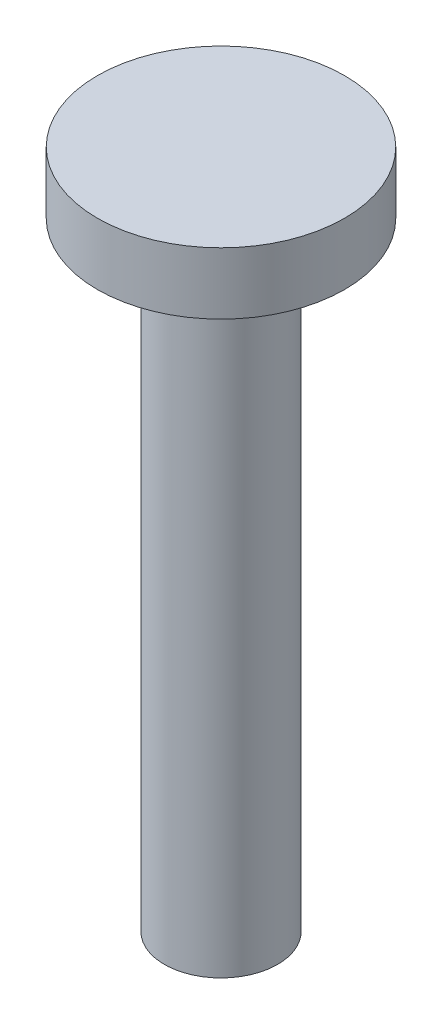
SolidWorks part; units mm, degrees
ref_plane "Front" through (0, 0, 0) normal (0, 0, 1) x (1, 0, 0)
ref_plane "Top" through (0, 0, 0) normal (0, 1, 0) x (1, 0, 0)
ref_plane "Right" through (0, 0, 0) normal (1, 0, 0) x (0, 0, -1)
sketch "Sketch1" plane through (0, 0, 0) normal (0, 1, 0) x (1, 0, 0)
  circle A0 centre (0, 0) radius 10
  dimension "D1" = 20
extrude "Boss-Extrude1" add sketch "Sketch1" along normal blind 90
scale "축척1" scale about centroid uniform scaling yes scale factor 0.3
sketch "스케치1" plane through (0, 58.5, 0) normal (0, 1, 0) x (1, 0, 0)
  circle A0 centre (0, 0) radius 6
  dimension "D1" = 12
extrude "보스-돌출1" add sketch "스케치1" along normal blind 3
sketch "스케치2" plane through (0, 31.5, 0) normal (0, -1, 0) x (1, 0, 0)
  circle A0 centre (0, 0) radius 3
  dimension "D1" = 6
extrude "보스-돌출3" add sketch "스케치2" along normal blind 3 contours A0
sketch "스케치3" plane through (0, 28.5, 0) normal (0, -1, 0) x (1, 0, 0)
  circle A0 centre (0, 0) radius 3
  circle A1 centre (0, 0) radius 2.75
  dimension "D1" = 5.5
extrude "컷-돌출2" cut sketch "스케치3" against normal up to surface (30 mm away) up to face at (0, 58.5, 3)
